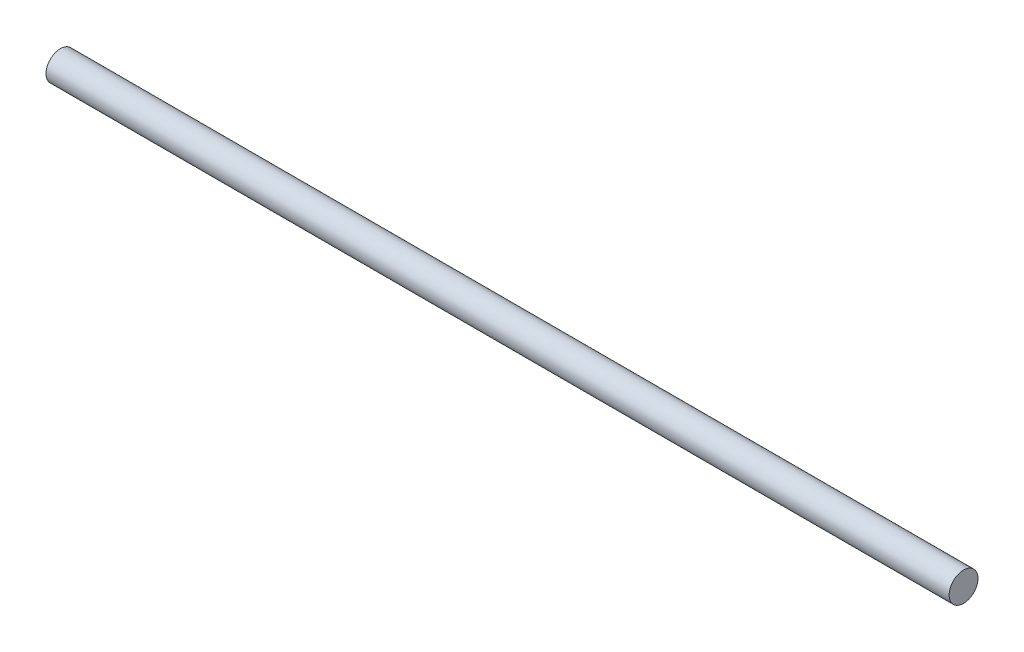
SolidWorks part; units mm, degrees
ref_plane "Front Plane" through (0, 0, 0) normal (0, 0, 1) x (1, 0, 0)
ref_plane "Top Plane" through (0, 0, 0) normal (0, 1, 0) x (1, 0, 0)
ref_plane "Right Plane" through (0, 0, 0) normal (1, 0, 0) x (0, 0, -1)
sketch "Sketch1" plane through (0, 0, 0) normal (1, 0, 0) x (0, 0, -1)
  circle A0 centre (0, 0) radius 2
  dimension "D1" = 4
extrude "Boss-Extrude1" add sketch "Sketch1" along normal mid plane 125
